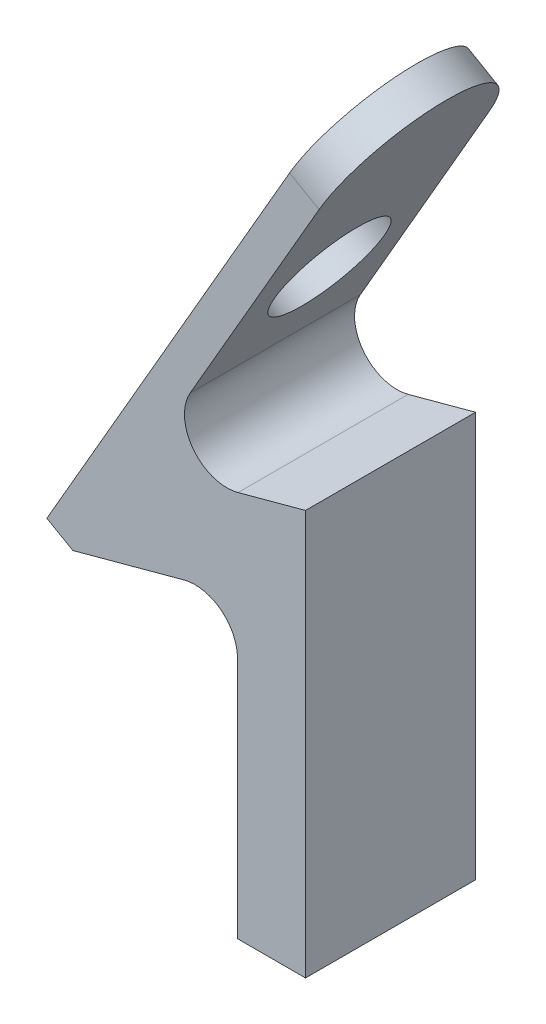
SolidWorks part; units mm, degrees
ref_plane "Plan de face" through (0, 0, 0) normal (0, 0, 1) x (1, 0, 0)
ref_plane "Plan de dessus" through (0, 0, 0) normal (0, 1, 0) x (1, 0, 0)
ref_plane "Plan de droite" through (0, 0, 0) normal (1, 0, 0) x (0, 0, -1)
sketch "Esquisse1" plane through (0, 0, 164.8705) normal (0, 0, 1) x (1, 0, 0)
  line L0 (-68.5886, 15.5026) -> (-68.5886, -32.6577) construction
  line L1 (-68.5886, 15.5026) -> (-68.5886, -32.6577)
  line L2 (-76.2359, 41.857) -> (-95.6859, 8.1686) construction
  line L3 (-72.4609, 48.3955) -> (-102.7748, -4.1098)
  line L4 (-68.5886, 15.5026) -> (-90.2117, 9.6502)
  line L5 (-68.5886, -32.6577) -> (-78.5886, -32.6577)
  line L6 (-78.5886, 15.5026) -> (-78.5886, 12.796)
  line L7 (-65.9761, 5.8498) -> (-68.5886, 5.1428)
  line L8 (-65.9761, 5.8498) -> (-93.0734, -1.4841) construction
  line L9 (-78.5886, 2.4363) -> (-102.7748, -4.1098)
  line L10 (-78.5886, 2.4363) -> (-78.5886, -32.6577)
  line L11 (-68.9968, 46.3955) -> (-90.2117, 9.6502)
  line L12 (-78.5886, 15.5026) -> (-78.5886, -32.6577) construction
  line L13 (-79.9087, 52.6955) -> (-77.7437, 51.4455) construction
  line L14 (-68.5886, 15.5026) -> (-95.6859, 8.1686) construction
  line L15 (-72.7718, 39.857) -> (-99.3107, -6.1098) construction
  line L16 (-72.4609, 48.3955) -> (-68.9968, 46.3955)
  line L17 (-76.2359, 41.857) -> (-102.7748, -4.1098) construction
  line M25 (-68.5886, 15.5026) -> (-68.5886, -32.6577)
  dimension "D1" = 10
  dimension "D2" = 10
  dimension "D3" = 4
extrude "Boss.-Extru.1" add sketch "Esquisse1" against normal blind 20 contours L16 L3 L9 L10 L5 L1 L4 L11 M25
fillet "Congé1" radius 5 2 edges at (-90.2117, 9.6502, 154.8705) (-78.5886, 2.4363, 154.8705)
chamfer "Chanfrein1" distance 5 angle 45 1 edges at (-102.7748, -4.1098, 154.8705)
sketch "Esquisse8" plane through (-75.3016, 43.4754, 0) normal (-0.866, 0.5, 0) x (0, 0, 1)
  line L0 (144.8705, 5.6813) -> (164.8705, 5.6813) construction
  line L1 (144.8705, 5.6813) -> (164.8705, 5.6813)
  arc A0 (144.8705, 5.6813) -> (164.8705, 5.6813) centre (154.8705, 5.6813) cw
extrude "Boss.-Extru.2" add sketch "Esquisse8" against normal up to surface (4 mm away) up to face at (-76.5757, 33.2685, 154.8705)
sketch "Esquisse9" plane through (-68.5886, 0, 0) normal (1, 0, 0) x (0, 0, -1)
  line L4 (-164.8705, 15.5026) -> (-164.8705, -32.6577)
  line L5 (-164.8705, -32.6577) -> (-144.8705, -32.6577)
  line L6 (-144.8705, -32.6577) -> (-144.8705, 15.5026)
  line L7 (-144.8705, 15.5026) -> (-164.8705, 15.5026)
  line L8 (-164.8705, 15.5026) -> (-164.8705, -32.6577)
  line L9 (-164.8705, -32.6577) -> (-144.8705, -32.6577)
  line L10 (-144.8705, -32.6577) -> (-144.8705, 15.5026)
  line L11 (-144.8705, 15.5026) -> (-164.8705, 15.5026)
  dimension "D1" = 0
extrude "Enlèv. mat.-Extru.5" cut sketch "Esquisse9" against normal blind 2
sketch "Esquisse10" plane through (-75.3016, 43.4754, 0) normal (-0.866, 0.5, 0) x (0, 0, 1)
  circle A1 centre (154.8705, -11.8687) radius 6.5
extrude "Enlèv. mat.-Extru.6" cut sketch "Esquisse10" against normal blind 4
